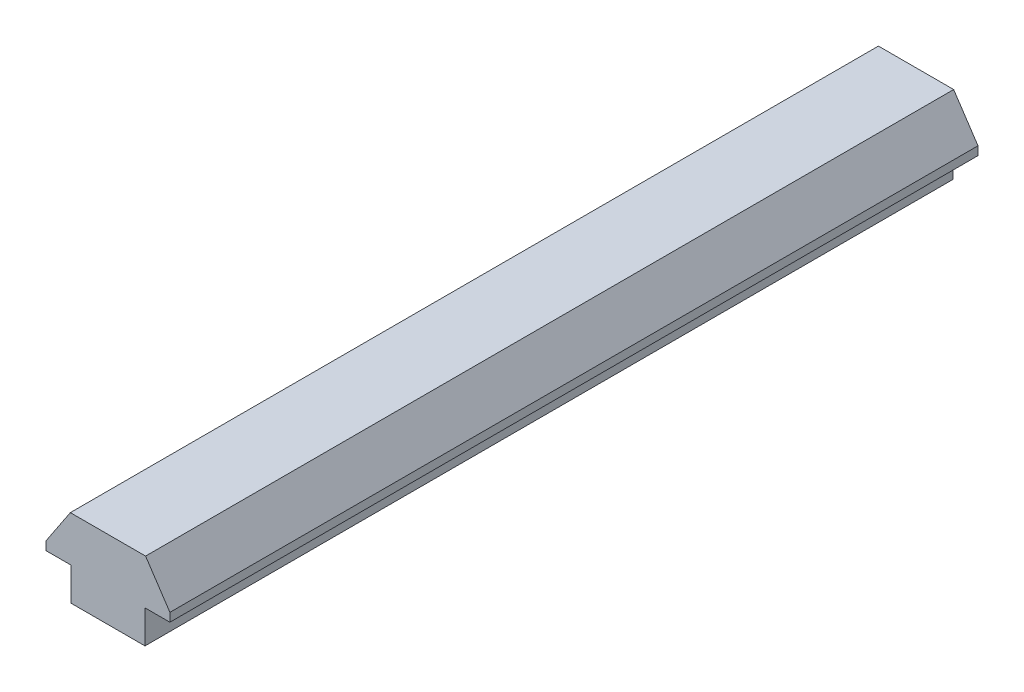
SolidWorks part; units mm, degrees
ref_plane "Front" through (0, 0, 0) normal (0, 0, 1) x (1, 0, 0)
ref_plane "Top" through (0, 0, 0) normal (0, 1, 0) x (1, 0, 0)
ref_plane "Right" through (0, 0, 0) normal (1, 0, 0) x (0, 0, -1)
sketch "Sketch1" plane through (0, 0, 0) normal (0, 0, 1) x (1, 0, 0)
  line L1 (-2.75, 2.45) -> (2.75, 2.45)
  line L2 (-2.75, 2.45) -> (-2.75, 0)
  line L3 (-2.75, 0) -> (2.75, 0)
  line L4 (2.75, 2.45) -> (2.75, 0)
  dimension "D1" = 5.5
  dimension "D2" = 2.45
extrude "Boss-Extrude1" add sketch "Sketch1" along normal up to surface (60 mm away)
sketch "Sketch2" plane through (0, 0, 0) normal (0, 0, 1) x (1, 0, 0)
  line L0 (-4.6, 2.45) -> (4.6, 2.45)
  line L1 (0, 0) -> (0, 2.45) construction
  line L2 (2.75, 2.45) -> (-2.75, 2.45) construction
  line L3 (-4.6, 2.45) -> (-4.6, 3.085)
  line L4 (-4.6, 3.085) -> (-2.794, 5.8)
  line L5 (-2.794, 5.8) -> (2.794, 5.8)
  line L6 (4.6, 3.085) -> (2.794, 5.8)
  line L7 (4.6, 2.45) -> (4.6, 3.085)
  point P11 (0, 5.8)
  dimension "D1" = 9.2
  dimension "D2" = 0.635
  dimension "D3" = 2.794
  dimension "D4" = 3.35
extrude "Boss-Extrude2" add sketch "Sketch2" along normal up to surface (60 mm away) up to face at (0.6875, 1.225, 60)
